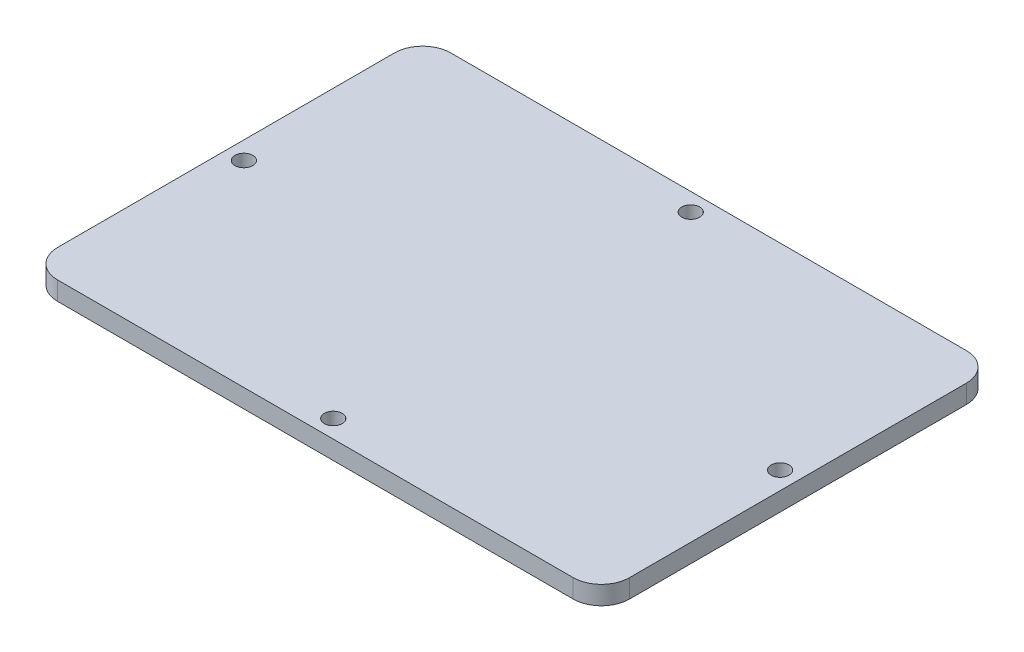
SolidWorks part; units mm, degrees
material "UHMW"
ref_plane "Front Plane" through (0, 0, 0) normal (0, 0, 1) x (1, 0, 0)
ref_plane "Top Plane" through (0, 0, 0) normal (0, 1, 0) x (1, 0, 0)
ref_plane "Right Plane" through (0, 0, 0) normal (1, 0, 0) x (0, 0, -1)
sketch "Sketch1" plane through (0, 0, 0) normal (0, 1, 0) x (1, 0, 0)
  line L1 (-50.8, -34.925) -> (50.8, -34.925)
  line L2 (-50.8, -34.925) -> (-50.8, 34.925)
  line L3 (-50.8, 34.925) -> (50.8, 34.925)
  line L4 (50.8, -34.925) -> (50.8, 34.925)
  line L5 (-50.8, -34.925) -> (50.8, 34.925) construction
  line L6 (-50.8, 34.925) -> (50.8, -34.925) construction
  point P0 (0, 0)
  dimension "D1" = 101.6
  dimension "D2" = 69.85
extrude "Boss-Extrude1" add sketch "Sketch1" along normal blind 3.302
sketch "Sketch4" plane through (0, 0, 0) normal (0, -1, 0) x (-1, 0, 0)
  circle A0 centre (0, 31.75) radius 1.5875
  circle A1 centre (-47.625, 0) radius 1.5875
  circle A2 centre (0, -31.75) radius 1.5875
  circle A3 centre (47.625, 0) radius 1.5875
  circle A8 centre (-47.625, 0) radius 1.5875 construction
  circle A9 centre (0, 31.75) radius 1.5875 construction
  circle A10 centre (0, -31.75) radius 1.5875 construction
  circle A11 centre (47.625, 0) radius 1.5875 construction
extrude "Cut-Extrude1" cut sketch "Sketch4" against normal through all
fillet "Fillet1" radius 5 4 edges at (50.8, 1.651, -34.925) (50.8, 1.651, 34.925) (-50.8, 1.651, 34.925) (-50.8, 1.651, -34.925)
